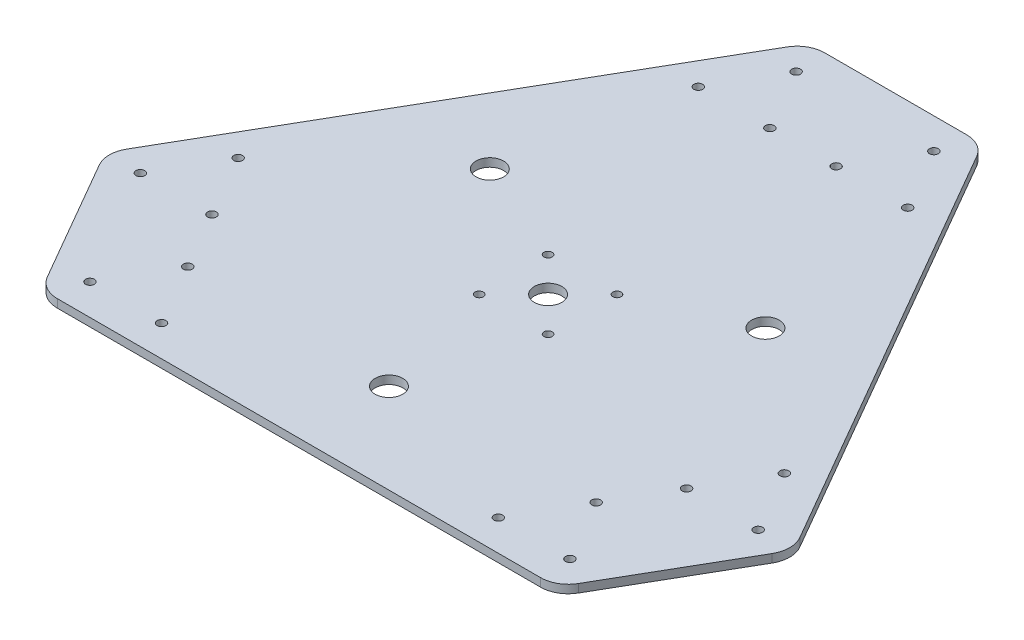
SolidWorks part; units mm, degrees
ref_plane "Front Plane" through (0, 0, 0) normal (0, 0, 1) x (1, 0, 0)
ref_plane "Top Plane" through (0, 0, 0) normal (0, 1, 0) x (1, 0, 0)
ref_plane "Right Plane" through (0, 0, 0) normal (1, 0, 0) x (0, 0, -1)
sketch "Sketch1" plane through (0, 0, 0) normal (0, 1, 0) x (1, 0, 0)
  line L0 (0, 0) -> (-31.5296, 126.1185) construction
  line L7 (0, 0) -> (31.5296, 126.1185) construction
  line L8 (0, 0) -> (0, 164.0632) construction
  line L18 (0, 0) -> (124.9867, -35.7538) construction
  line L19 (0, 0) -> (142.0829, -82.0316) construction
  line L20 (0, 0) -> (93.457, -90.3647) construction
  line L21 (0, 0) -> (-93.457, -90.3647) construction
  line L22 (0, 0) -> (-142.0829, -82.0316) construction
  line L23 (0, 0) -> (-124.9867, -35.7538) construction
  line L24 (-31.5296, 126.1185) -> (31.5296, 126.1185)
  line L25 (31.5296, 126.1185) -> (124.9867, -35.7538)
  line L26 (124.9867, -35.7538) -> (93.457, -90.3647)
  line L27 (93.457, -90.3647) -> (-93.457, -90.3647)
  line L28 (-93.457, -90.3647) -> (-124.9867, -35.7538)
  line L29 (-124.9867, -35.7538) -> (-31.5296, 126.1185)
  line L31 (-12.0096, 92.5) -> (-25, 115) construction
  line L32 (-25, 115) -> (-37.9904, 92.5) construction
  line L33 (-37.9904, 92.5) -> (-12.0096, 92.5) construction
  circle A1 centre (0, 0) radius 130 construction
  circle A8 centre (-25, 100) radius 7.5 construction
  circle A9 centre (-25, 115) radius 1.6
  circle A10 centre (-12.0096, 92.5) radius 1.6
  circle A11 centre (-37.9904, 92.5) radius 1.6
  circle A12 centre (37.9904, 92.5) radius 1.6
  circle A13 centre (12.0096, 92.5) radius 1.6
  circle A14 centre (25, 115) radius 1.6
  circle A15 centre (112.0929, -35.8494) radius 1.6
  circle A16 centre (86.1122, -35.8494) radius 1.6
  circle A17 centre (99.1025, -13.3494) radius 1.6
  circle A18 centre (74.1025, -56.6506) radius 1.6
  circle A19 centre (87.0929, -79.1506) radius 1.6
  circle A20 centre (61.1122, -79.1506) radius 1.6
  circle A21 centre (-87.0929, -79.1506) radius 1.6
  circle A22 centre (-74.1025, -56.6506) radius 1.6
  circle A23 centre (-61.1122, -79.1506) radius 1.6
  circle A24 centre (-86.1122, -35.8494) radius 1.6
  circle A25 centre (-112.0929, -35.8494) radius 1.6
  circle A26 centre (-99.1025, -13.3494) radius 1.6
  point P17 (0, 0)
  point P31 (0, 0)
  point P66 (0, 0)
  dimension "D1" = 130
  dimension "D2" = 100
  dimension "D8" = 3.2
  dimension "D3" = 3
  dimension "D4" = 25
  dimension "D7" = 15
  dimension "D9" = 3
extrude "Boss-Extrude1" add sketch "Sketch1" along normal blind 3
sketch "Sketch2" plane through (0, 3, 0) normal (0, 1, 0) x (1, 0, 0)
  spline S0 degree 3 poles (-21.8278, -2.2812) (-12.6823, -9.9378) (-6.7958, 0.4199) (0.6953, 3.1342) knots 0 0 0 0 1 1 1 1
  spline S1 degree 3 poles (-21.8278, -2.2812) (-12.8155, -6.5924) (-7.2747, 2.0376) (0.6953, 3.1342) knots 0 0 0 0 1 1 1 1
  spline S2 degree 3 poles (-18.2726, -5.542) (-10.2008, -7.8915) (-2.143, 4.2124) (13.1546, 4.7414) (17.6735, -0.7547) knots 0 0 0 0 0.516039 1 1 1 1
  spline S3 degree 3 poles (-18.2726, -5.542) (-10.413, -10.8182) (-1.9481, 0.7095) (12.5093, 3.2347) (17.6735, -0.7547) knots 0 0 0 0 0.521405 1 1 1 1
  spline S4 degree 3 poles (-9.7807, -8.2706) (-0.9227, -5.8315) (5.4716, 4.8113) (16.3637, -1.885) knots 0 0 0 0 1 1 1 1
  spline S5 degree 3 poles (-9.7807, -8.2706) (-0.1733, -8.1763) (5.6934, 2.388) (16.3637, -1.885) knots 0 0 0 0 1 1 1 1
  spline S6 degree 3 poles (-3.4514, -8.0585) (2.0503, -5.9492) (8.4216, -0.0015) (14.8828, -3.417) knots 0 0 0 0 1 1 1 1
  spline S7 degree 3 poles (-3.4514, -8.0585) (3.0711, -7.633) (7.9554, -1.7723) (14.8828, -3.417) knots 0 0 0 0 1 1 1 1
extrude "Cut-Extrude1" [suppressed] cut sketch "Sketch2" against normal through all
sketch "Sketch3" plane through (0, 3, 0) normal (0, 1, 0) x (1, 0, 0)
  line L0 (-93.457, -90.3647) -> (93.457, -90.3647) construction
  line L1 (-12.5, -12.5) -> (12.5, -12.5) construction
  line L2 (-12.5, -12.5) -> (-12.5, 12.5) construction
  line L3 (-12.5, 12.5) -> (12.5, 12.5) construction
  line L4 (12.5, -12.5) -> (12.5, 12.5) construction
  line L5 (-12.5, -12.5) -> (12.5, 12.5) construction
  line L6 (-12.5, 12.5) -> (12.5, -12.5) construction
  line L7 (50, 28.8675) -> (-50, 28.8675) construction
  line L8 (-50, 28.8675) -> (0, -57.735) construction
  line L9 (0, -57.735) -> (50, 28.8675) construction
  circle A0 centre (-12.5, 12.5) radius 1.5
  circle A1 centre (12.5, 12.5) radius 1.5
  circle A2 centre (12.5, -12.5) radius 1.5
  circle A3 centre (-12.5, -12.5) radius 1.5
  circle A4 centre (0, 0) radius 28.8675 construction
  circle A5 centre (-50, 28.8675) radius 5
  circle A6 centre (50, 28.8675) radius 5
  circle A7 centre (0, -57.735) radius 5
  circle A8 centre (0, 0) radius 5
  point P0 (0, 0)
  dimension "D2" = 3
  dimension "D4" = 10
  dimension "D1" = 25
  dimension "D3" = 100
extrude "Cut-Extrude2" cut sketch "Sketch3" against normal through all
fillet "Fillet1" radius 10 6 edges at (93.457, 1.5, 90.3647) (124.9867, 1.5, 35.7538) (31.5296, 1.5, -126.1185) (-31.5296, 1.5, -126.1185) (-124.9867, 1.5, 35.7538) (-93.457, 1.5, 90.3647)
